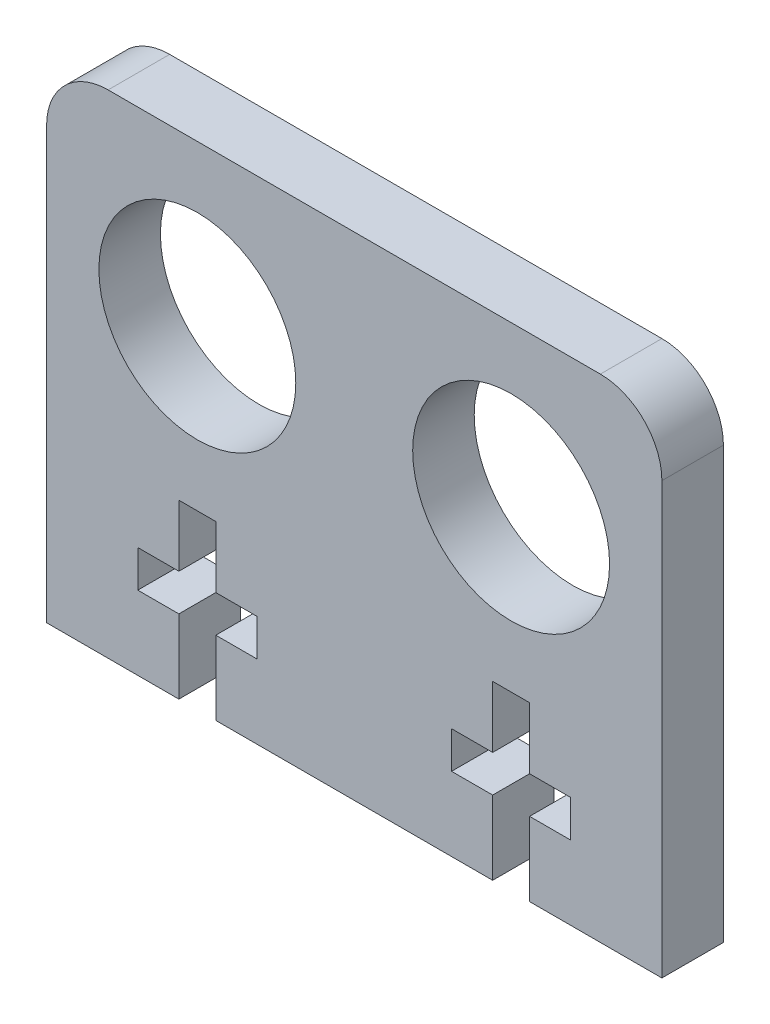
SolidWorks part; units mm, degrees
ref_plane "Piano frontale" through (0, 0, 0) normal (0, 0, 1) x (1, 0, 0)
ref_plane "Piano superiore" through (0, 0, 0) normal (0, 1, 0) x (1, 0, 0)
ref_plane "Piano destro" through (0, 0, 0) normal (1, 0, 0) x (0, 0, -1)
sketch "Sketch1" plane through (0, 0, 0) normal (0, 0, 1) x (1, 0, 0)
  line L0 (-18.9895, -13.2336) -> (31.0105, -13.2336)
  line L1 (31.0105, -13.2336) -> (31.0105, 26.7664)
  line L2 (31.0105, 26.7664) -> (-18.9895, 26.7664)
  line L3 (-18.9895, 26.7664) -> (-18.9895, -13.2336)
  line L4 (6.0105, -13.2336) -> (6.0105, 41.9567) construction
  dimension "D1" = 50
  dimension "D2" = 40
extrude "Boss-Extrude1" add sketch "Sketch1" along normal blind 5
sketch "Sketch2" plane through (0, 0, 0) normal (0, 0, -1) x (-1, 0, 0)
  line L0 (-18.7601, 13.7664) -> (6.7399, 13.7664) construction
  line L2 (-31.0105, 26.7664) -> (18.9895, 26.7664) construction
  line L3 (-6.0105, 26.7664) -> (-6.0105, -13.2336) construction
  line L4 (18.9895, -13.2336) -> (-31.0105, -13.2336) construction
  circle A0 centre (-18.7601, 13.7664) radius 8
  circle A1 centre (6.7399, 13.7664) radius 8
  dimension "D1" = 16
  dimension "D2" = 25.5
  dimension "D3" = 13
extrude "Cut-Extrude1" cut sketch "Sketch2" against normal blind 5
sketch "Sketch3" plane through (0, 0, 5) normal (0, 0, 1) x (1, 0, 0)
  line L0 (-6.7399, 13.7664) -> (-6.7399, -43.2902) construction
  line L1 (18.7601, 13.7664) -> (18.7601, -43.2902) construction
  line L12 (-18.9895, -13.2336) -> (31.0105, -13.2336) construction
  line L13 (17.2601, -13.2336) -> (20.2601, -13.2336)
  line L14 (17.2601, -13.2336) -> (17.2601, -7.2336)
  line L15 (17.2601, -7.2336) -> (13.9201, -7.2336)
  line L16 (13.9201, -7.2336) -> (13.9201, -4.2336)
  line L17 (13.9201, -4.2336) -> (17.2601, -4.2336)
  line L18 (17.2601, -4.2336) -> (17.2601, 0.7664)
  line L19 (17.2601, 0.7664) -> (20.2601, 0.7664)
  line L20 (20.2601, 0.7664) -> (20.2601, -4.2336)
  line L21 (20.2601, -4.2336) -> (23.6001, -4.2336)
  line L22 (23.6001, -4.2336) -> (23.6001, -7.2336)
  line L23 (23.6001, -7.2336) -> (20.2601, -7.2336)
  line L24 (20.2601, -7.2336) -> (20.2601, -13.2336)
  line L26 (-8.2399, -13.2336) -> (-5.2399, -13.2336)
  line L27 (-8.2399, -13.2336) -> (-8.2399, -7.2336)
  line L28 (-8.2399, -7.2336) -> (-11.5799, -7.2336)
  line L29 (-11.5799, -7.2336) -> (-11.5799, -4.2336)
  line L30 (-11.5799, -4.2336) -> (-8.2399, -4.2336)
  line L31 (-8.2399, -4.2336) -> (-8.2399, 0.7664)
  line L32 (-8.2399, 0.7664) -> (-5.2399, 0.7664)
  line L33 (-5.2399, 0.7664) -> (-5.2399, -4.2336)
  line L34 (-5.2399, -4.2336) -> (-1.8999, -4.2336)
  line L35 (-1.8999, -4.2336) -> (-1.8999, -7.2336)
  line L36 (-1.8999, -7.2336) -> (-5.2399, -7.2336)
  line L37 (-5.2399, -7.2336) -> (-5.2399, -13.2336)
  point P5 (-6.7399, -13.2336)
  point P6 (18.7601, -13.2336)
  dimension "D6" = 3
  dimension "D7" = 6
  dimension "D8" = 5
  dimension "D9" = 3
  dimension "D10" = 3.34
  dimension "D12" = 3
  dimension "D13" = 6
  dimension "D14" = 5
  dimension "D15" = 3
  dimension "D16" = 3.34
extrude "Cut-Extrude2" cut sketch "Sketch3" against normal blind 10
fillet "Fillet1" radius 5 1 edges at (-18.9895, 26.7664, 2.5)
fillet "Fillet2" radius 5 1 edges at (31.0105, 26.7664, 2.5)
